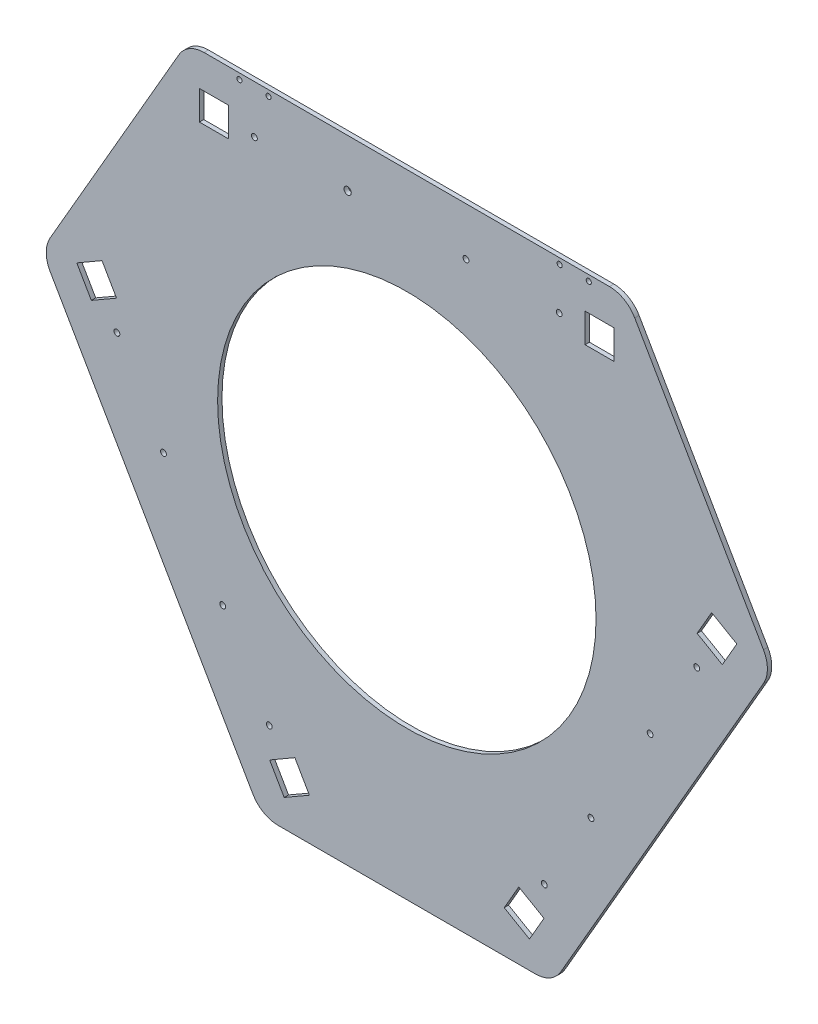
SolidWorks part; units mm, degrees
ref_plane "前视基准面" through (0, 0, 0) normal (0, 0, 1) x (1, 0, 0)
ref_plane "上视基准面" through (0, 0, 0) normal (0, 1, 0) x (1, 0, 0)
ref_plane "右视基准面" through (0, 0, 0) normal (1, 0, 0) x (0, 0, -1)
other "Configuration Table"
sketch "草图1" plane through (0, 0, 0) normal (0, 0, 1) x (1, 0, 0)
  line L0 (150.8286, 202.551) -> (-150.8286, 202.551)
  line L1 (-150.8286, 202.551) -> (-250.8286, 29.3459)
  line L2 (-250.8286, 29.3459) -> (-100, -231.8969)
  line L3 (-100, -231.8969) -> (100, -231.8969)
  line L4 (100, -231.8969) -> (250.8286, 29.3459)
  line L6 (-200.8286, 115.9485) -> (175.4143, -101.2755) construction
  line L7 (0, 202.551) -> (0, -231.8969) construction
  line L8 (-175.4143, -101.2755) -> (200.8262, 115.9471)
  line L9 (150.8286, 202.551) -> (250.8286, 29.3459)
  circle A0 centre (0, 0) radius 130
  circle A1 centre (-199.1913, 5.9076) radius 2 construction
  circle A2 centre (-167.1689, -49.5569) radius 2 construction
  circle A3 centre (-126.502, -119.9941) radius 2 construction
  circle A4 centre (-94.4796, -175.4585) radius 2 construction
  circle A5 centre (199.1913, 5.9076) radius 2 construction
  circle A6 centre (167.1689, -49.5569) radius 2 construction
  circle A7 centre (126.502, -119.9941) radius 2 construction
  circle A8 centre (94.4796, -175.4585) radius 2 construction
  circle A9 centre (104.7118, 169.551) radius 2 construction
  circle A10 centre (40.6669, 169.551) radius 2 construction
  circle A11 centre (-40.6669, 169.551) radius 2.5 construction
  circle A12 centre (-104.7118, 169.551) radius 2 construction
  circle A13 centre (-199.1913, 5.9076) radius 2
  circle A14 centre (-167.1689, -49.5569) radius 2
  circle A15 centre (-126.502, -119.9941) radius 2
  circle A16 centre (-94.4796, -175.4585) radius 2
  circle A17 centre (199.1913, 5.9076) radius 2
  circle A18 centre (167.1689, -49.5569) radius 2
  circle A19 centre (126.502, -119.9941) radius 2
  circle A20 centre (94.4796, -175.4585) radius 2
  circle A21 centre (104.7118, 169.551) radius 2
  circle A22 centre (40.6669, 169.551) radius 2
  circle A23 centre (-40.6669, 169.551) radius 2.5
  circle A24 centre (-104.7118, 169.551) radius 2
  circle A25 centre (125, 198.551) radius 1.75
  circle A26 centre (105, 198.551) radius 1.75
  circle A27 centre (-95, 198.551) radius 1.75
  circle A28 centre (-115, 198.551) radius 1.75
  point P7 (0, 0)
  point P70 (-122.2962, -44.0868)
  dimension "D7" = 3.5
  dimension "D3" = 260
  dimension "D1" = 120
  dimension "D2" = 120
  dimension "D4" = 3.5
  dimension "D5" = 3.5
  dimension "D6" = 200
  dimension "D8" = 3.5
extrude "凸台-拉伸1" add sketch "草图1" along normal blind 3
sketch "草图8" plane through (0, 0, 3) normal (0, 0, 1) x (1, 0, 0)
  line L0 (-142.5, 179.551) -> (-142.5, 159.551)
  line L1 (-142.5, 179.551) -> (-122.5, 179.551)
  line L2 (-142.5, 159.551) -> (-122.5, 159.551)
  line L3 (-122.5, 179.551) -> (-122.5, 159.551)
  line L4 (-175.4143, -101.2755) -> (0, 0)
  line L5 (-209.4252, 43.6331) -> (-226.7457, 33.6331)
  line L6 (-209.4252, 43.6331) -> (-199.4252, 26.3126)
  line L7 (-226.7457, 33.6331) -> (-216.7457, 16.3126)
  line L8 (-199.4252, 26.3126) -> (-216.7457, 16.3126)
  line L9 (-84.2457, -213.1841) -> (-66.9252, -203.1841)
  line L10 (-84.2457, -213.1841) -> (-94.2457, -195.8636)
  line L11 (-66.9252, -203.1841) -> (-76.9252, -185.8636)
  line L12 (-94.2457, -195.8636) -> (-76.9252, -185.8636)
  line L13 (66.9252, -203.1841) -> (84.2457, -213.1841)
  line L14 (66.9252, -203.1841) -> (76.9252, -185.8636)
  line L15 (84.2457, -213.1841) -> (94.2457, -195.8636)
  line L16 (76.9252, -185.8636) -> (94.2457, -195.8636)
  line L17 (209.4252, 43.6331) -> (199.4252, 26.3126)
  line L18 (209.4252, 43.6331) -> (226.7457, 33.6331)
  line L19 (199.4252, 26.3126) -> (216.7457, 16.3126)
  line L20 (226.7457, 33.6331) -> (216.7457, 16.3126)
  line L21 (142.5, 179.551) -> (142.5, 159.551)
  line L22 (142.5, 179.551) -> (122.5, 179.551)
  line L23 (142.5, 159.551) -> (122.5, 159.551)
  line L24 (122.5, 179.551) -> (122.5, 159.551)
  line L25 (0, 0) -> (175.4143, -101.2755)
  line L26 (0, 202.551) -> (0, 0)
  line L28 (150.8286, 202.551) -> (-150.8286, 202.551) construction
  line L29 (100, -231.8969) -> (250.8286, 29.3459) construction
  line L31 (-250.8286, 29.3459) -> (-100, -231.8969) construction
  dimension "D1" = 20
  dimension "D2" = 20
  dimension "D3" = 20
  dimension "D4" = 20
  dimension "D5" = 20
  dimension "D6" = 20
  dimension "D7" = 20
  dimension "D8" = 20
  dimension "D9" = 20
  dimension "D10" = 20
  dimension "D11" = 23
  dimension "D12" = 245
  dimension "D13" = 245
  dimension "D14" = 23
  dimension "D15" = 245
  dimension "D16" = 23
  dimension "D17" = 122.5
  dimension "D18" = 122.5
  dimension "D19" = 122.5
  dimension "D21" = 20
  dimension "D22" = 20
extrude "切除-拉伸4" cut sketch "草图8" against normal through all contours L0 L1 L3 L2 | L5 L6 L8 L7 | L21 L22 L24 L23 | L17 L18 L20 L19 | L9 L10 L12 L11 | L13 L14 L16 L15
fillet "圆角2" radius 20 6 edges at (100, -231.8969, 1.5) (-100, -231.8969, 1.5) (150.8286, 202.551, 1.5) (250.8286, 29.3459, 1.5) (-250.8286, 29.3459, 1.5) (-150.8286, 202.551, 1.5)
